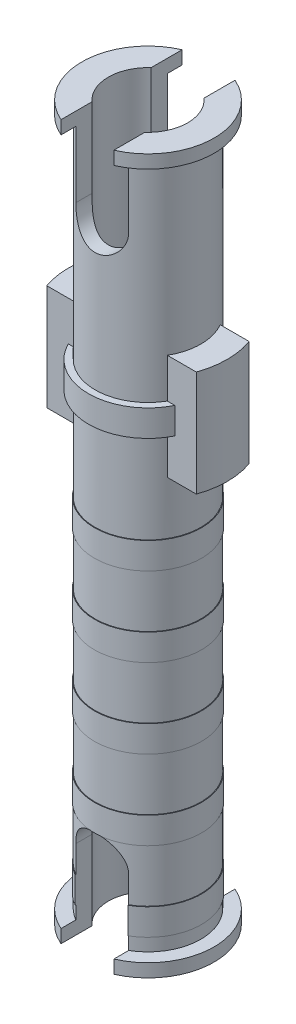
SolidWorks part; units mm, degrees
material "PBT General Purpose"
ref_plane "Front Plane" through (0, 0, 0) normal (0, 0, 1) x (1, 0, 0)
ref_plane "Top Plane" through (0, 0, 0) normal (0, 1, 0) x (1, 0, 0)
ref_plane "Right Plane" through (0, 0, 0) normal (1, 0, 0) x (0, 0, -1)
sketch "Sketch1" plane through (0, 0, 0) normal (0, 0, 1) x (1, 0, 0)
  line L0 (0, 13.5) -> (0, -13.5) construction
  line L1 (-2, 13.5) -> (0, 13.5)
  line L3 (-2, -13.5) -> (-2, 13.5)
  line L6 (-2, -13.5) -> (0, -13.5)
  line L7 (0, 13.5) -> (0, -13.5)
  line L9 (0, 13.5) -> (-2.5, 13.5)
  line L10 (0, 13.5) -> (0, 13)
  line L11 (0, 13) -> (-2.5, 13)
  line L12 (-2.5, 13.5) -> (-2.5, 13)
  line L13 (0, -13.5) -> (-2.5, -13.5)
  line L14 (0, -13.5) -> (0, -13)
  line L15 (0, -13) -> (-2.5, -13)
  line L16 (-2.5, -13.5) -> (-2.5, -13)
  line L17 (0, 4) -> (-2.25, 4)
  line L18 (0, 4) -> (0, 5)
  line L19 (0, 5) -> (-2.25, 5)
  line L20 (-2.25, 4) -> (-2.25, 5)
  point P3 (0, 0)
  point P16 (-2.25, 4.5)
  dimension "D1" = 27
  dimension "D2" = 2
  dimension "D3" = 2.5
  dimension "D4" = 0.5
  dimension "D5" = 1
  dimension "D6" = 2.25
  dimension "D7" = 9
revolve "Revolve5" add sketch "Sketch1" angle 360 about L0
sketch "Sketch3" plane through (0, 0, 0) normal (0, 0, 1) x (1, 0, 0)
  line L0 (2.25, 4.5) -> (-2.25, 4.5) construction
  line L1 (2.25, 4) -> (2.25, 5) construction
  line L2 (-2.25, 5) -> (-2.25, 4) construction
  line L4 (-3, 2.5) -> (3, 2.5)
  line L5 (-3, 2.5) -> (-3, 6.5)
  line L6 (-3, 6.5) -> (3, 6.5)
  line L7 (3, 2.5) -> (3, 6.5)
  line L8 (2, 5) -> (2, 13) construction
  point P12 (0, 4.5)
  point P13 (3, 4.5)
  dimension "D1" = 4
  dimension "D2" = 6
  dimension "D3" = 1
extrude "Boss-Extrude4" add sketch "Sketch3" along normal mid plane 2
sketch "Sketch7" plane through (0, 0, 0) normal (0, 0, 1) x (1, 0, 0)
  line L5 (0, 5) -> (0, -4.6052) construction
  line L6 (2.0156, 5) -> (-2.0156, 5) construction
  line L7 (-3, 2.5) -> (-1.7321, 2.5) construction
  line L9 (0, -0.5042) -> (-2.025, -0.5042)
  line L10 (0, -0.5042) -> (0, 0.4958)
  line L11 (0, 0.4958) -> (-2.025, 0.4958)
  line L12 (-2.025, -0.5042) -> (-2.025, 0.4958)
  dimension "D1" = 1
  dimension "D2" = 2.025
  dimension "D3" = 2.0042
revolve "Revolve7" add sketch "Sketch7" angle 360 about L5
pattern_linear "LPattern1" count 5 spacing 3 along (0, -1, 0) of "Revolve7"
sketch "Sketch5" plane through (0, 0, 0) normal (0, 0, 1) x (1, 0, 0)
  line L0 (-1, 13.5) -> (-1, 10.5)
  line L1 (2.5, 13.5) -> (-2.5, 13.5) construction
  line L2 (1, 10.5) -> (1, 13.5)
  line L3 (1, 13.5) -> (-1, 13.5)
  line L8 (-1, -13.5) -> (-1, -10.5)
  line L9 (-2.5, -13.5) -> (2.5, -13.5) construction
  line L10 (1, -10.5) -> (1, -13.5)
  line L11 (1, -13.5) -> (-1, -13.5)
  arc A0 (-1, 10.5) -> (1, 10.5) centre (0, 10.5) ccw
  arc A2 (-1, -10.5) -> (1, -10.5) centre (0, -10.5) cw
  dimension "D1" = 1
  dimension "D2" = 3
extrude "Cut-Extrude2" cut sketch "Sketch5" against normal through all both and the other way through all
sketch "Sketch6" plane through (0, 13.5, 0) normal (0, 1, 0) x (1, 0, 0)
  circle A0 centre (0, 0) radius 1.5
  dimension "D1" = 3
extrude "Cut-Extrude3" cut sketch "Sketch6" against normal up to surface (27 mm away) up to face at (-1.75, -13.5, 0)
sketch "Sketch8" plane through (0, 0, 0) normal (0, 1, 0) x (1, 0, 0)
  circle A0 centre (0, 0) radius 3
  dimension "D1" = 6
extrude "Cut-Extrude4" cut sketch "Sketch8" against normal through all both and the other way through all flip side to cut
